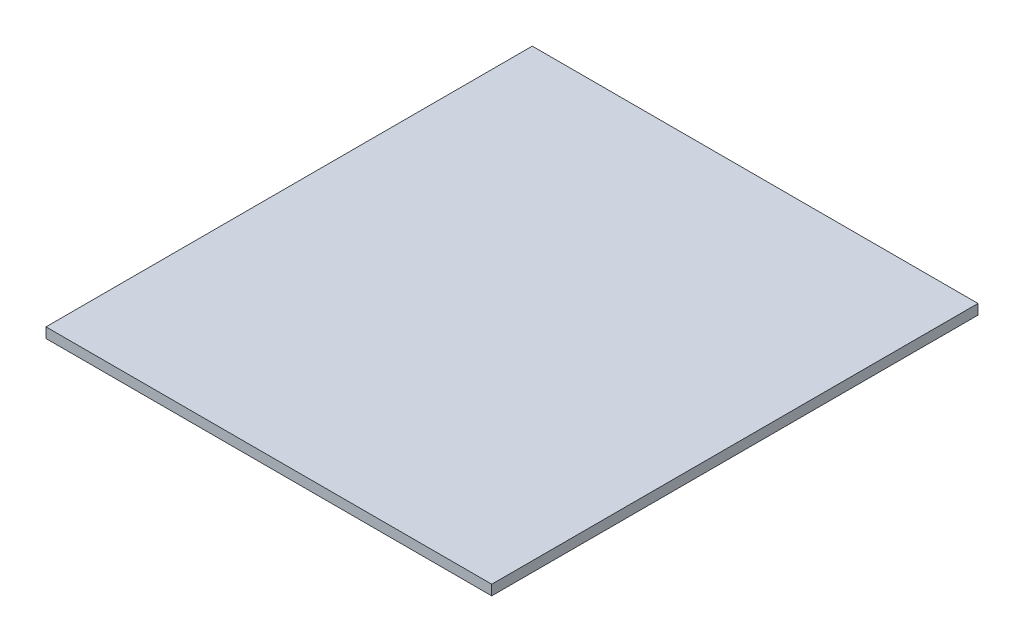
SolidWorks part; units mm, degrees
ref_plane "Front Plane" through (0, 0, 0) normal (0, 0, 1) x (1, 0, 0)
ref_plane "Top Plane" through (0, 0, 0) normal (0, 1, 0) x (1, 0, 0)
ref_plane "Right Plane" through (0, 0, 0) normal (1, 0, 0) x (0, 0, -1)
sketch "Sketch1" plane through (0, 0, 0) normal (0, 1, 0) x (1, 0, 0)
  line L1 (-44, 48) -> (44, 48)
  line L2 (-44, 48) -> (-44, -48)
  line L3 (-44, -48) -> (44, -48)
  line L4 (44, 48) -> (44, -48)
  line L5 (-44, 48) -> (44, -48) construction
  line L6 (-44, -48) -> (44, 48) construction
  point P0 (0, 0)
  dimension "D1" = 96
  dimension "D2" = 88
extrude "Boss-Extrude1" add sketch "Sketch1" along normal blind 2 contours L2 L3 L4 L1
sketch "Sketch2" plane through (0, 0, 0) normal (0, -1, 0) x (1, 0, 0)
  line L0 (0, -48) -> (0, 48) construction
  line L1 (-44, -48) -> (44, -48) construction
  line L2 (-44, 48) -> (44, 48) construction
  line L3 (0, 48) -> (0, 0) construction
  line L4 (0, 0) -> (102.0764, 0) construction
